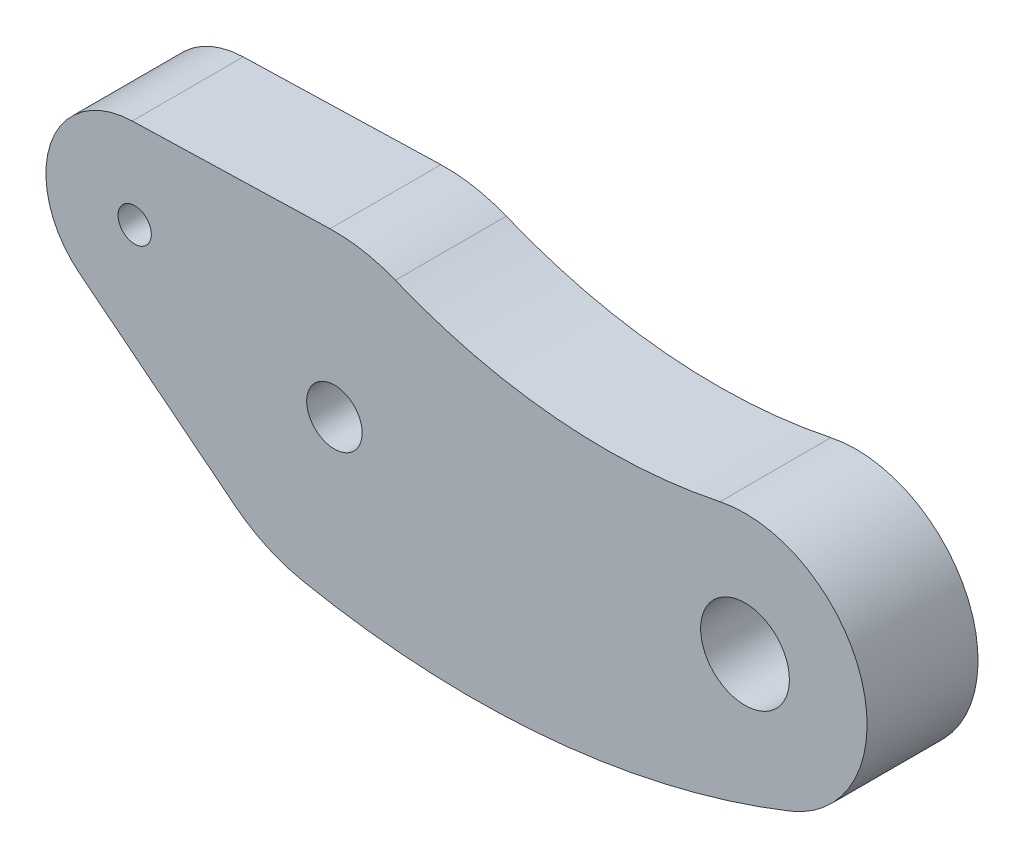
SolidWorks part; units mm, degrees
material "PMMA"
ref_plane "Front Plane" through (0, 0, 0) normal (0, 0, 1) x (1, 0, 0)
ref_plane "Top Plane" through (0, 0, 0) normal (0, 1, 0) x (1, 0, 0)
ref_plane "Right Plane" through (0, 0, 0) normal (1, 0, 0) x (0, 0, -1)
sketch "Sketch1" plane through (0, 0, 0) normal (0, 0, 1) x (1, 0, 0)
  line L0 (0, 0) -> (18.5, 0) construction
  line L1 (-11.4884, -0.1318) -> (-4.5102, -5.6763)
  line L2 (-9.1116, 6.9984) -> (-0.2023, 7.2472)
  circle A0 centre (0, 0) radius 1.25
  circle A1 centre (18.5, 0) radius 2
  arc A2 (20.5334, -5.1103) -> (17.3697, 5.3826) centre (18.5, 0) ccw
  arc A3 (2.7436, 6.7108) -> (-0.2023, 7.2472) centre (0, 0) ccw
  circle A4 centre (-9, 3) radius 0.75
  arc A5 (-9.1116, 6.9984) -> (-11.4884, -0.1318) centre (-9, 3) ccw
  arc A6 (-1.4193, -7.1097) -> (20.5334, -5.1103) centre (6.1806, 30.9617) ccw
  arc A7 (2.7436, 6.7108) -> (17.3697, 5.3826) centre (12.2224, 29.8953) ccw
  arc A8 (-4.5102, -5.6763) -> (-1.4193, -7.1097) centre (0, 0) ccw
  dimension "D1" = 2.5
  dimension "D3" = 4
  dimension "D4" = 11
  dimension "D5" = 14.5
  dimension "D6" = 1.5
  dimension "D9" = 8
  dimension "D2" = 18.5
  dimension "D7" = 3
  dimension "D8" = 9
  dimension "D10" = 7.1097
  dimension "D11" = 6.7108
extrude "Boss-Extrude1" add sketch "Sketch1" along normal blind 5
cosmetic thread "Cosmetic Thread1" parameters "D2"=3
cosmetic thread "Cosmetic Thread2" parameters "D2"=2
